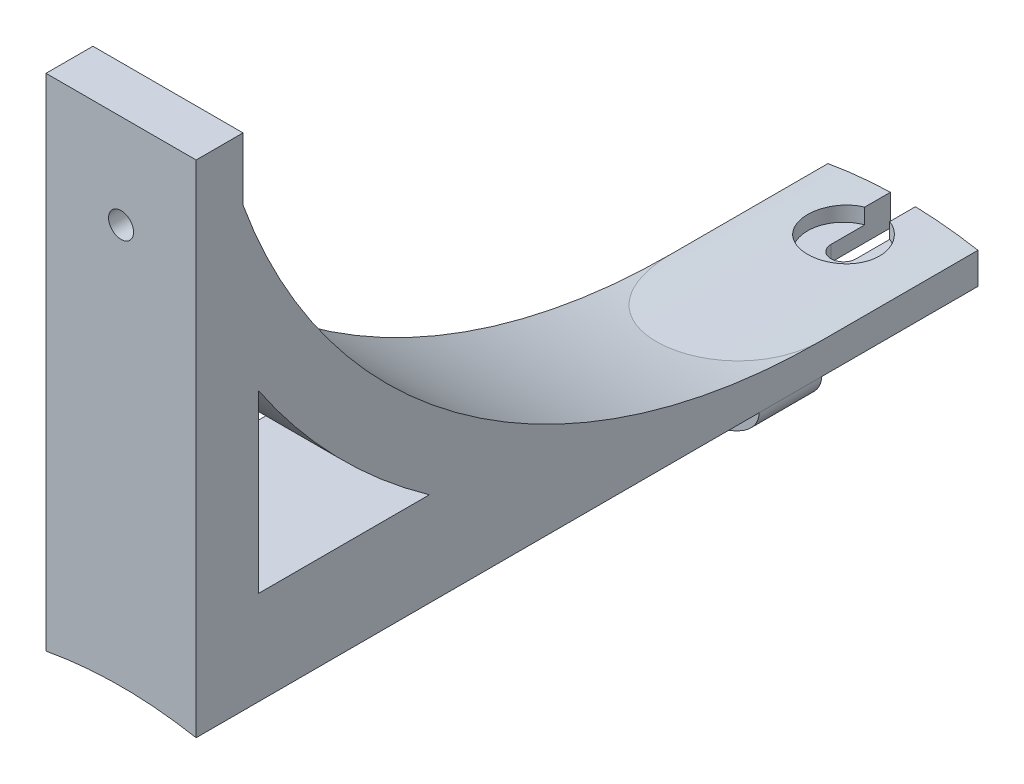
SolidWorks part; units mm, degrees
ref_plane "Front Plane" through (0, 0, 0) normal (0, 0, 1) x (1, 0, 0)
ref_plane "Top Plane" through (0, 0, 0) normal (0, 1, 0) x (1, 0, 0)
ref_plane "Right Plane" through (0, 0, 0) normal (1, 0, 0) x (0, 0, -1)
sketch "Sketch1" plane through (0, 0, 0) normal (0, 0, 1) x (1, 0, 0)
  line L0 (-12, 69.1371) -> (-12, 64.1371)
  line L1 (12, 69.1371) -> (12, 64.1371)
  line L2 (-2, 68.2207) -> (-2, 65.2193) construction
  line L3 (2, 65.2193) -> (2, 68.2207) construction
  line L4 (-2, 68.2207) -> (-2, 65.2193) construction
  line L5 (2, 65.2193) -> (2, 68.2207) construction
  line L6 (-2, 66.72) -> (2, 66.72) construction
  circle A0 centre (0, 0) radius 65.25 construction
  arc A2 (12, 64.1371) -> (-12, 64.1371) centre (0, 0) ccw
  arc A3 (12, 69.1371) -> (-12, 69.1371) centre (0, 1.9503) ccw
  dimension "D3" = 5
  dimension "D1" = 10
  dimension "D2" = 10
extrude "Boss-Extrude1" add sketch "Sketch1" along normal blind 100 and the other way blind 25
sketch "Sketch2" plane through (0, 0, 0) normal (0, 0, 1) x (1, 0, 0)
  line L0 (12, 64.1371) -> (-12, 64.1371) construction
  arc A0 (12, 64.1371) -> (-12, 64.1371) centre (0, 0) ccw construction
  arc A1 (12, 64.1371) -> (-12, 64.1371) centre (0, 0) ccw
  arc A2 (12, 69.1371) -> (-12, 69.1371) centre (0, 1.9503) ccw construction
  ellipse E0 centre (0, 64.1371) end of major axis (12, 64.1371) minor radius 6.0632 (-12, 64.1371) -> (12, 64.1371) ccw
  point P18 (0, 70.2003)
extrude "Boss-Extrude2" add sketch "Sketch2" along normal blind 10
sketch "Sketch3" plane through (-12, 0, 0) normal (-1, 0, 0) x (0, 0, 1)
  line L0 (-25, 69.1371) -> (0, 69.1371) construction
  line L1 (-25, 69.1371) -> (100, 69.1371) construction
  line L2 (92.5, 134.1371) -> (92.5, 144.1371)
  line L3 (100, 69.1371) -> (100, 144.1371)
  line L4 (92.5, 144.1371) -> (100, 144.1371)
  line L5 (100, 69.1371) -> (0, 69.1371)
  line L6 (90, 79.1371) -> (90, 107.183)
  line L7 (90, 107.183) -> (90, 107.183)
  line L8 (90, 107.183) -> (90, 107.183)
  line L9 (90, 79.1371) -> (62.7112, 79.1371)
  arc A0 (0, 69.1371) -> (92.5, 134.1371) centre (0, 167.4544) ccw
  arc A1 (62.7112, 79.1371) -> (90, 107.183) centre (0, 167.4544) ccw
  dimension "D1" = 7.5
  dimension "D2" = 10
  dimension "D3" = 75
  dimension "D4" = 10
extrude "Boss-Extrude4" add sketch "Sketch3" against normal up to surface (24 mm away) up to face at (12, 65.8037, 26.6667)
sketch "Sketch5" plane through (0, 0, -25) normal (0, 0, -1) x (-1, 0, 0)
  line L0 (0, 65.25) -> (0, 70.2003) construction
  arc A0 (12, 64.1371) -> (-12, 64.1371) centre (0, 0) ccw construction
  arc A1 (12, 69.1371) -> (-12, 69.1371) centre (0, 1.9503) ccw construction
ref_plane "Plane1" through (0, 70.2003, -25) normal (0, 1, 0) x (1, 0, 0)
sketch "Sketch8" plane through (0, 70.2003, -25) normal (0, 1, 0) x (1, 0, 0)
  line L0 (2, -9.5) -> (2, 0)
  line L1 (12, 0) -> (-12, 0) construction
  line L2 (2, 0) -> (-2, 0)
  line L3 (-2, 0) -> (-2, -9.5)
  circle A0 centre (0, -9.5) radius 2 construction
  arc A1 (-2, -9.5) -> (2, -9.5) centre (0, -9.5) ccw
extrude "Cut-Extrude3" cut sketch "Sketch8" against normal through all both and the other way through all
sketch "Sketch9" plane through (0, 70.2003, -25) normal (0, 1, 0) x (1, 0, 0)
  circle A0 centre (0, -9.5) radius 5.75
  dimension "D1" = 11.5
extrude "Cut-Extrude4" cut sketch "Sketch9" against normal blind 2.5
sketch "Sketch10" plane through (0, 0, 92.5) normal (0, 0, -1) x (-1, 0, 0)
  line L0 (0, 144.1371) -> (0, 129.1371) construction
  line L1 (-12, 144.1371) -> (12, 144.1371) construction
  circle A0 centre (0, 129.1371) radius 2
  dimension "D2" = 4
  dimension "D1" = 15
extrude "Cut-Extrude5" cut sketch "Sketch10" against normal through all both and the other way through all
sketch "Sketch11" plane through (0, 0, 92.5) normal (0, 0, -1) x (-1, 0, 0)
  circle A2 centre (0, 129.1371) radius 4.5
  circle A3 centre (0, 129.1371) radius 4.5
  dimension "D1" = 2.5
extrude "Cut-Extrude6" cut sketch "Sketch11" along normal through all
